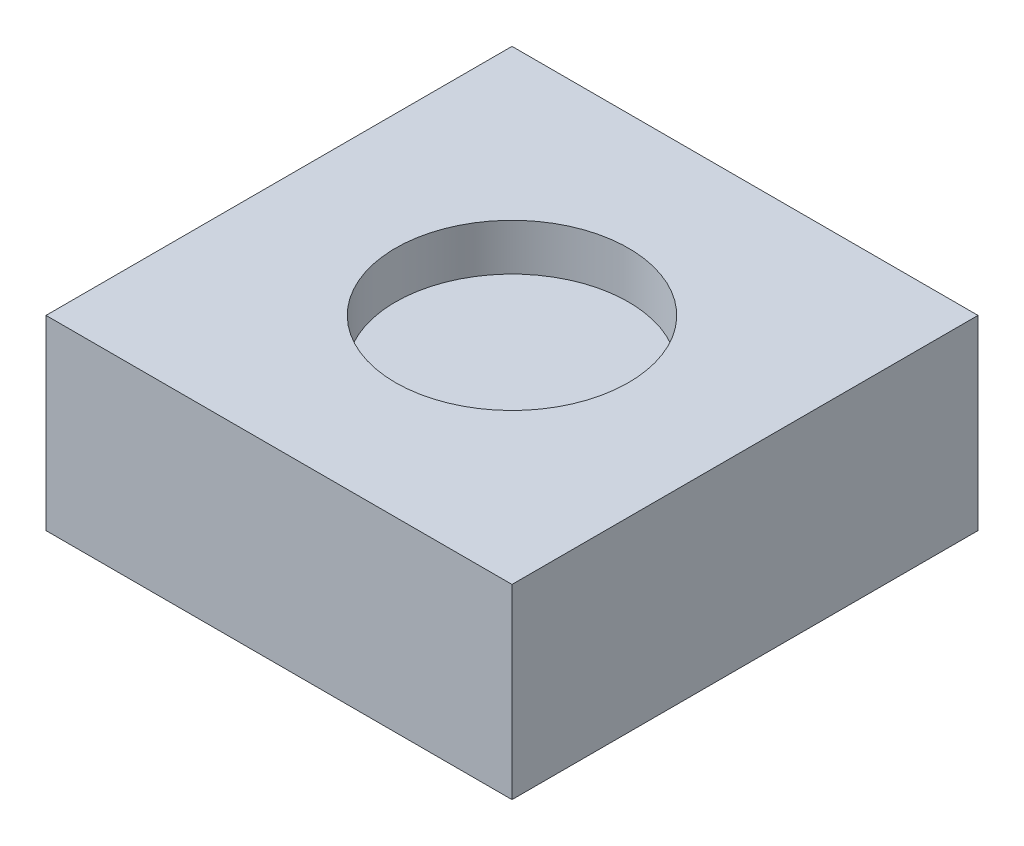
SolidWorks part; units mm, degrees
ref_plane "Front Plane" through (0, 0, 0) normal (0, 0, 1) x (1, 0, 0)
ref_plane "Top Plane" through (0, 0, 0) normal (0, 1, 0) x (1, 0, 0)
ref_plane "Right Plane" through (0, 0, 0) normal (1, 0, 0) x (0, 0, -1)
sketch "Sketch1" plane through (0, 0, 0) normal (0, 1, 0) x (1, 0, 0)
  line L1 (-10, -10) -> (10, -10)
  line L2 (-10, -10) -> (-10, 10)
  line L3 (-10, 10) -> (10, 10)
  line L4 (10, -10) -> (10, 10)
  line L5 (-10, -10) -> (10, 10) construction
  line L6 (-10, 10) -> (10, -10) construction
  point P0 (0, 0)
  dimension "D1" = 20
  dimension "D2" = 20
extrude "Boss-Extrude1" add sketch "Sketch1" along normal blind 8
sketch "Sketch2" plane through (0, 8, 0) normal (0, 1, 0) x (1, 0, 0)
  circle A0 centre (0, 0) radius 5
  dimension "D1" = 10
extrude "Cut-Extrude1" cut sketch "Sketch2" against normal blind 2
sketch "Sketch3" plane through (0, 0, 0) normal (0, -1, 0) x (1, 0, 0)
  circle A0 centre (0, 0) radius 1
  dimension "D1" = 2
extrude "Cut-Extrude2" cut sketch "Sketch3" against normal blind 2
fillet "Fillet1" radius 1 1 edges at (0, 2, -1)
